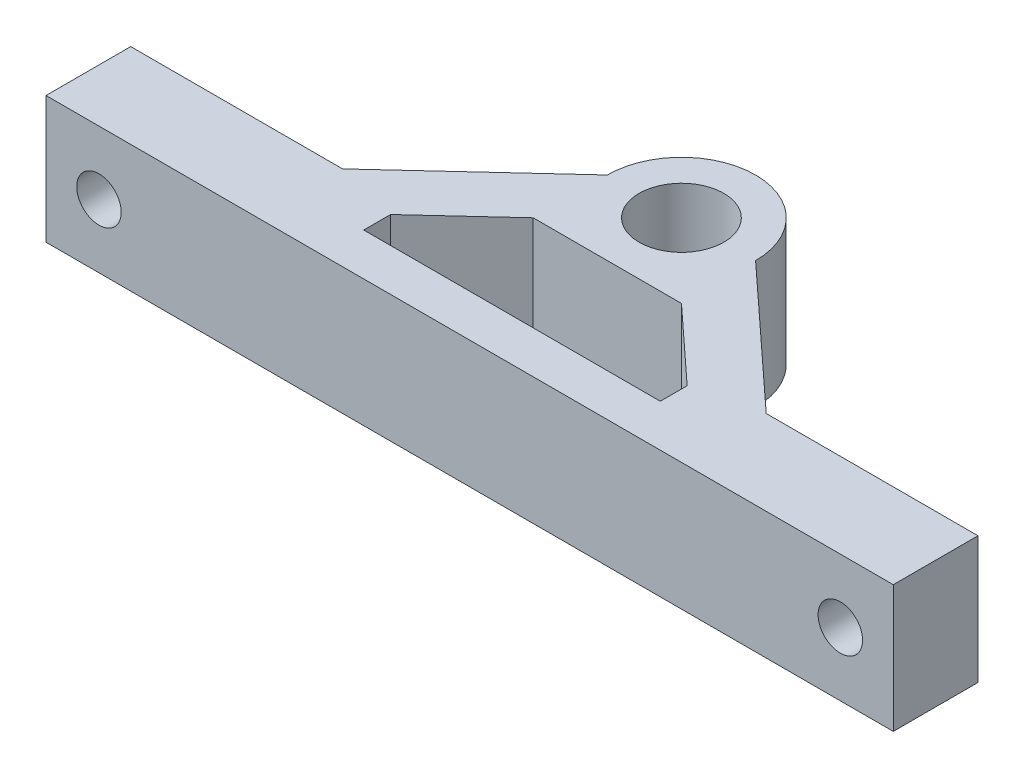
SolidWorks part; units mm, degrees
ref_plane "Спереди" through (0, 0, 0) normal (0, 0, 1) x (1, 0, 0)
ref_plane "Сверху" through (0, 0, 0) normal (0, 1, 0) x (1, 0, 0)
ref_plane "Справа" through (0, 0, 0) normal (1, 0, 0) x (0, 0, -1)
sketch "Эскиз1" plane through (0, 0, 0) normal (0, 1, 0) x (1, 0, 0)
  line L0 (0, 0) -> (0, -40) construction
  line L1 (-40, -20) -> (40, -20)
  line L2 (-40, -20) -> (-40, -12)
  line L3 (-40, -12) -> (-20, -12)
  line L4 (-20, -12) -> (-7, 0)
  line L5 (40, -20) -> (40, -12)
  line L6 (40, -12) -> (20, -12)
  line L7 (20, -12) -> (7, 0)
  line L8 (-14, -16) -> (14, -16)
  line L9 (14, -16) -> (14, -13.4615)
  line L10 (14, -13.4615) -> (7, -7)
  line L11 (7, -7) -> (-7, -7)
  line L12 (-7, -7) -> (-14, -13.4615)
  line L13 (-14, -13.4615) -> (-14, -16)
  circle A0 centre (0, 0) radius 4
  arc A1 (7, 0) -> (-7, 0) centre (0, 0) ccw
  point P7 (0, -20)
  point P19 (0, -16)
  point P23 (0, -7)
  dimension "D1" = 80
  dimension "D2" = 8
  dimension "D3" = 14
  dimension "D4" = 20
  dimension "D5" = 8
  dimension "D6" = 8
  dimension "D7" = 20
  dimension "D8" = 20
  dimension "D9" = 28
  dimension "D10" = 14
  dimension "D11" = 4
  dimension "D12" = 9
extrude "Бобышка-Вытянуть1" add sketch "Эскиз1" along normal blind 12
hole_wizard "Сверло под метчик  спиральное M41" positions "Эскиз2" profile "Эскиз3" hole size "M4x0.7" standard "DIN"
sketch "Эскиз2" plane through (0, 0, 20) normal (0, 0, 1) x (1, 0, 0)
  line L0 (-40, 12) -> (40, 12) construction
  line L1 (0, 0) -> (0, 19.9155) construction
  line L2 (-40, 0) -> (40, 0) construction
  point P0 (-35, 6)
  point P5 (35, 6)
  point P14 (0, 0)
  dimension "D1" = 6
  dimension "D2" = 70
  dimension "D3" = 35
sketch "Эскиз3" plane through (-35, 6, 20) normal (1, 0, 0) x (0, -1, 0)
  line L0 (0, 0) -> (0, 9.2618)
  line L1 (0, 9.2618) -> (2.1, 8)
  line L2 (2.1, 8) -> (2.1, 0)
  line L5 (2.1, 0) -> (0, 0)
  line L10 (0, 9.2618) -> (-2.1, 8) construction
  line L11 (0, -6.35) -> (0, 107.95) construction
  dimension "Диаметр отверстия" = 4.2
  dimension "Глубина отверстия" = 8
  dimension "Угол заточки сверла" = 118
